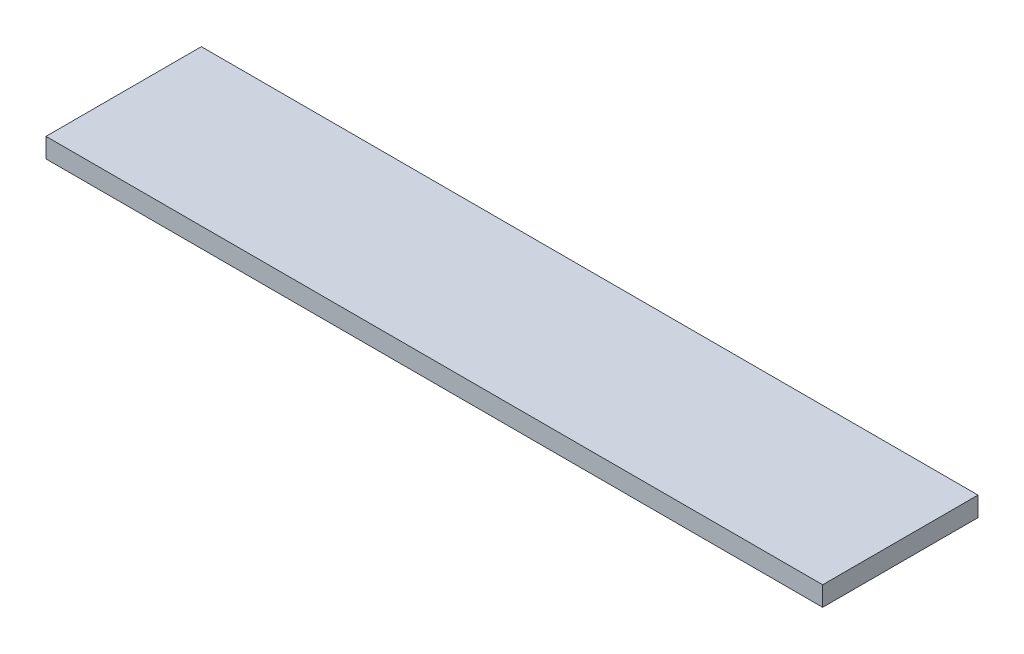
SolidWorks part; units mm, degrees
ref_plane "Front Plane" through (0, 0, 0) normal (0, 0, 1) x (1, 0, 0)
ref_plane "Top Plane" through (0, 0, 0) normal (0, 1, 0) x (1, 0, 0)
ref_plane "Right Plane" through (0, 0, 0) normal (1, 0, 0) x (0, 0, -1)
sketch "Sketch1" plane through (0, 0, 0) normal (0, 1, 0) x (1, 0, 0)
  line L1 (31.75, -6.35) -> (-31.75, -6.35)
  line L2 (31.75, -6.35) -> (31.75, 6.35)
  line L3 (31.75, 6.35) -> (-31.75, 6.35)
  line L4 (-31.75, -6.35) -> (-31.75, 6.35)
  line L5 (31.75, -6.35) -> (-31.75, 6.35) construction
  line L6 (31.75, 6.35) -> (-31.75, -6.35) construction
  point P0 (0, 0)
  dimension "D1" = 12.7
  dimension "D2" = 63.5
extrude "Boss-Extrude1" add sketch "Sketch1" along normal blind 1.6002
